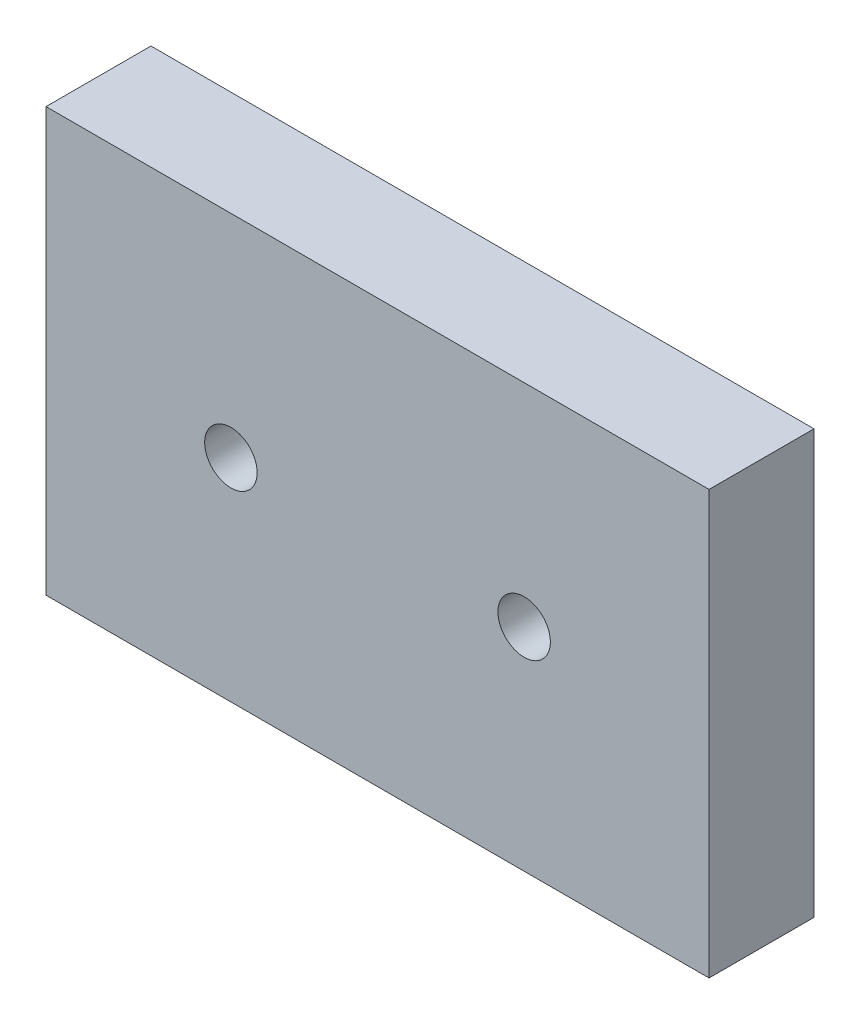
SolidWorks part; units mm, degrees
ref_plane "Front Plane" through (0, 0, 0) normal (0, 0, 1) x (1, 0, 0)
ref_plane "Top Plane" through (0, 0, 0) normal (0, 1, 0) x (1, 0, 0)
ref_plane "Right Plane" through (0, 0, 0) normal (1, 0, 0) x (0, 0, -1)
sketch "Sketch1" plane through (0, 0, 0) normal (0, 0, 1) x (1, 0, 0)
  line L8 (-10, 30.32) -> (-10, -10)
  line L9 (53.18, 30.32) -> (-10, 30.32)
  line L10 (53.18, -10) -> (53.18, 30.32)
  line L11 (-10, -10) -> (53.18, -10)
  line L12 (-10, 30.32) -> (-10, -10)
  line L13 (53.18, 30.32) -> (-10, 30.32)
  line L14 (53.18, -10) -> (53.18, 30.32)
  line L15 (-10, -10) -> (53.18, -10)
  circle A0 centre (35.56, 10.16) radius 2.5
  circle A1 centre (7.62, 10.16) radius 2.5
  dimension "D2" = 5
  dimension "D1" = 10
extrude "Boss-Extrude1" add sketch "Sketch1" along normal blind 10
